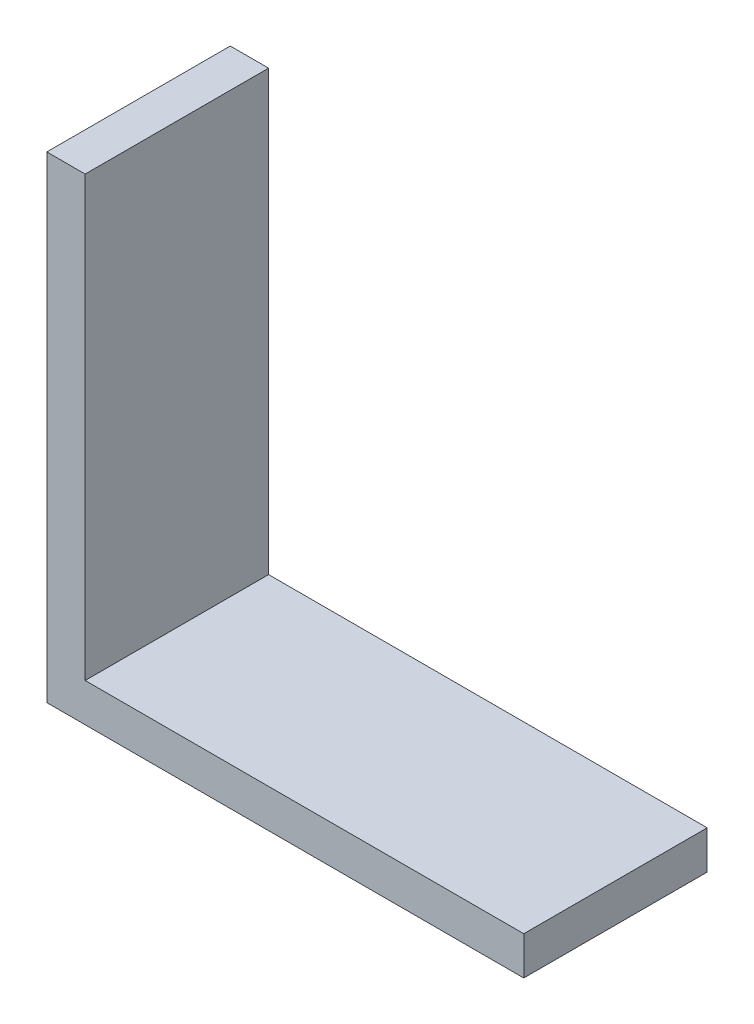
SolidWorks part; units mm, degrees
ref_plane "Front Plane" through (0, 0, 0) normal (0, 0, 1) x (1, 0, 0)
ref_plane "Top Plane" through (0, 0, 0) normal (0, 1, 0) x (1, 0, 0)
ref_plane "Right Plane" through (0, 0, 0) normal (1, 0, 0) x (0, 0, -1)
sketch "Sketch1" plane through (0, 0, 0) normal (0, 1, 0) x (1, 0, 0)
  line L1 (15.4781, -5.9531) -> (-15.4781, -5.9531)
  line L2 (15.4781, -5.9531) -> (15.4781, 5.9531)
  line L3 (15.4781, 5.9531) -> (-15.4781, 5.9531)
  line L4 (-15.4781, -5.9531) -> (-15.4781, 5.9531)
  line L5 (15.4781, -5.9531) -> (-15.4781, 5.9531) construction
  line L6 (15.4781, 5.9531) -> (-15.4781, -5.9531) construction
  point P0 (0, 0)
  dimension "D1" = 30.9562
  dimension "D2" = 11.9062
extrude "Boss-Extrude1" add sketch "Sketch1" along normal blind 2.4892
sketch "Sketch2" plane through (0, 0, 0) normal (0, 1, 0) x (1, 0, 0)
  line L0 (-15.4781, 5.9531) -> (-12.9889, 5.9531)
  line L1 (-12.9889, 5.9531) -> (-12.9889, -5.9531)
  line L2 (-15.4781, 5.9531) -> (-15.4781, -5.9531)
  line L3 (-15.4781, -5.9531) -> (15.4781, -5.9531) construction
  line L4 (-12.9889, -5.9531) -> (-15.4781, -5.9531)
  dimension "D1" = 2.4892
extrude "Boss-Extrude2" add sketch "Sketch2" along normal blind 30.9562
